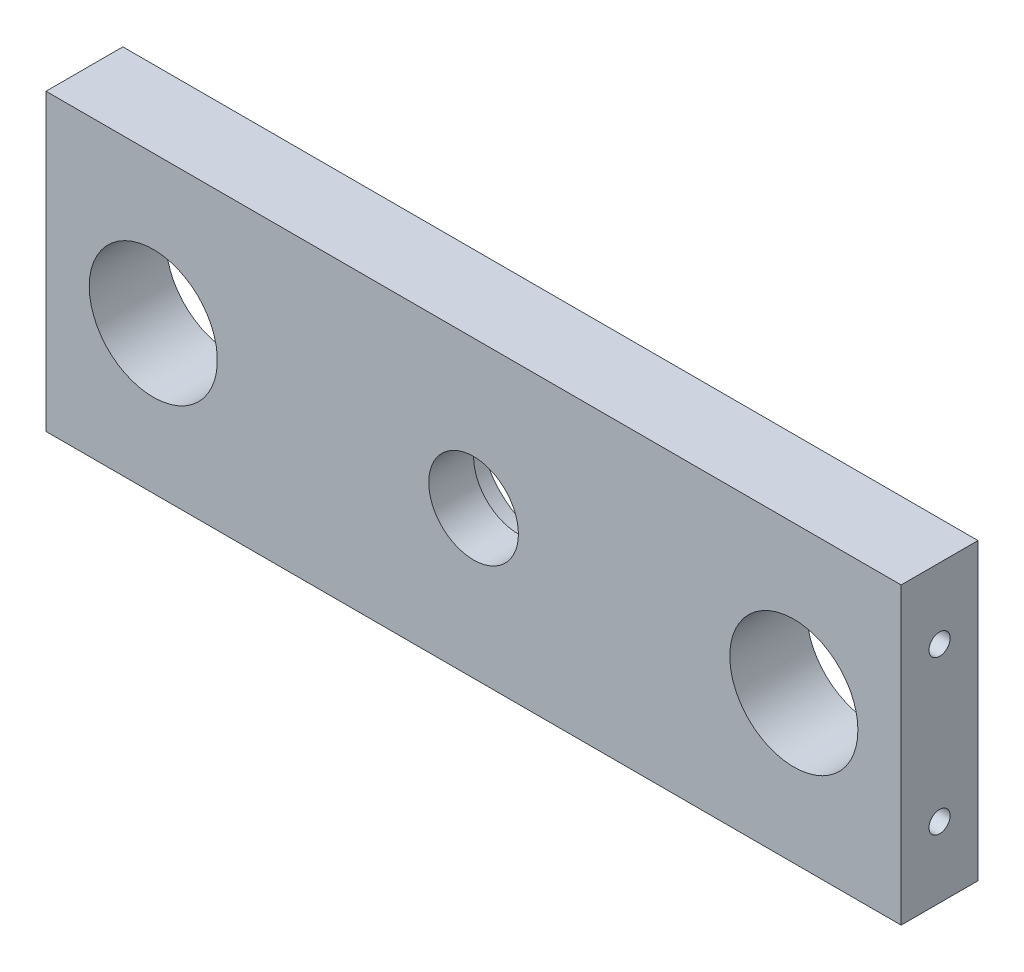
SolidWorks part; units mm, degrees
ref_plane "Front Plane" through (0, 0, 0) normal (0, 0, 1) x (1, 0, 0)
ref_plane "Top Plane" through (0, 0, 0) normal (0, 1, 0) x (1, 0, 0)
ref_plane "Right Plane" through (0, 0, 0) normal (1, 0, 0) x (0, 0, -1)
sketch "Sketch1" plane through (0, 0, 0) normal (0, 0, 1) x (1, 0, 0)
  line L0 (0, 0) -> (0, 22.3067) construction
  line L1 (0, 0) -> (50, 0) construction
  line L3 (-66.75, 23) -> (66.75, 23)
  line L4 (-66.75, 23) -> (-66.75, -23)
  line L5 (-66.75, -23) -> (66.75, -23)
  line L6 (66.75, 23) -> (66.75, -23)
  circle A0 centre (50, 0) radius 10
  circle A1 centre (-50, 0) radius 10
  circle A2 centre (0, 0) radius 7
  dimension "D3" = 20
  dimension "D5" = 14
  dimension "D1" = 46
  dimension "D2" = 133.5
  dimension "D4" = 100
extrude "Boss-Extrude1" add sketch "Sketch1" along normal blind 12
sketch "Sketch2" plane through (0, 0, 0) normal (0, 0, -1) x (-1, 0, 0)
  circle A0 centre (0, 0) radius 11
  dimension "D1" = 22
extrude "Cut-Extrude1" cut sketch "Sketch2" against normal blind 5
hole_wizard "M4 Tapped Hole1" positions "Sketch4" profile "Sketch5" tap size "M4" standard "ISO" end condition through all
sketch "Sketch4" plane through (-66.75, 0, 0) normal (-1, 0, 0) x (0, 0, 1)
  line L0 (0, 0) -> (12, 0) construction
  line L1 (0, 23) -> (0, -23) construction
  line L2 (12, 23) -> (12, -23) construction
  line L5 (6, 0) -> (6, 12) construction
  point P0 (6, 12)
  point P16 (0, 0)
  point P17 (6, -12)
  dimension "D1" = 24
sketch "Sketch5" plane through (-66.75, 12, 6) normal (0, 1, 0) x (0, 0, 1)
  line L0 (0, 0) -> (0, 133.5)
  line L1 (0, 133.5) -> (1.65, 133.5)
  line L2 (1.65, 133.5) -> (1.65, 0)
  line L5 (1.65, 0) -> (0, 0)
  line L11 (0, -6.35) -> (0, 107.95) construction
  dimension "Thru Tap Drill Dia." = 3.3
  dimension "Thru Tap Drill Depth" = 133.5
cosmetic thread "Hole Thread1" parameters "D2"=4
cosmetic thread "Hole Thread2" parameters "D2"=4
mirror "Mirror1" about plane through (0, 0, 0) normal (1, 0, 0) of "M4 Tapped Hole1"
